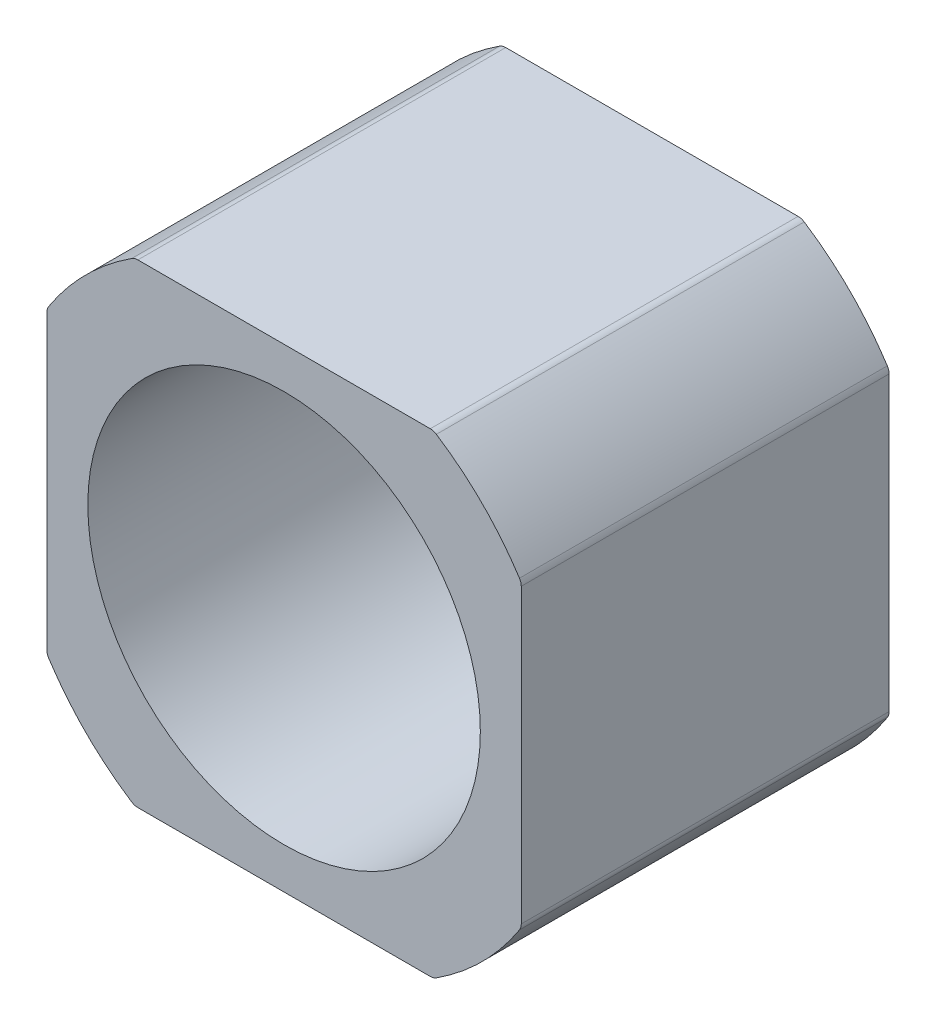
SolidWorks part; units mm, degrees
material "Acero aleado"
ref_plane "Alzado" through (0, 0, 0) normal (0, 0, 1) x (1, 0, 0)
ref_plane "Planta" through (0, 0, 0) normal (0, 1, 0) x (1, 0, 0)
ref_plane "Vista lateral" through (0, 0, 0) normal (1, 0, 0) x (0, 0, -1)
sketch "Croquis1" plane through (0, 0, 0) normal (0, 0, 1) x (1, 0, 0)
  line L0 (-21.15, 21.15) -> (21.15, 21.15)
  line L1 (-21.15, -21.15) -> (21.15, -21.15)
  line L2 (-21.15, 21.15) -> (-21.15, -21.15)
  line L4 (21.15, 21.15) -> (21.15, -21.15)
  line L5 (-21.15, 21.15) -> (21.15, -21.15) construction
  line L6 (-21.15, -21.15) -> (21.15, 21.15) construction
  point P0 (0, 0)
  point P6 (20.9601, -20.7736)
  point P7 (-21.2645, -21.0343)
  dimension "D1" = 42.3
  dimension "D2" = 42.3
extrude "Saliente-Extruir1" add sketch "Croquis1" along normal blind 32.8
sketch "Sketch1" plane through (0, 0, 32.8) normal (0, 0, 1) x (1, 0, 0)
  circle A0 centre (0, 0) radius 25
  circle A1 centre (0, 0) radius 29.9106
  dimension "D1" = 50
extrude "Cut-Extrude1" cut sketch "Sketch1" against normal through all
fillet "Fillet1" radius 1 8 edges at (13.3296, 21.15, 16.4) (-13.3296, 21.15, 16.4) (-21.15, 13.3296, 16.4) (-21.15, -13.3296, 16.4) (-13.3296, -21.15, 16.4) (13.3296, -21.15, 16.4) (21.15, -13.3296, 16.4) (21.15, 13.3296, 16.4)
sketch "Sketch2" plane through (0, 0, 32.8) normal (0, 0, 1) x (1, 0, 0)
  circle A0 centre (0, 0) radius 17.5
  dimension "D1" = 35
extrude "Cut-Extrude2" cut sketch "Sketch2" against normal through all
